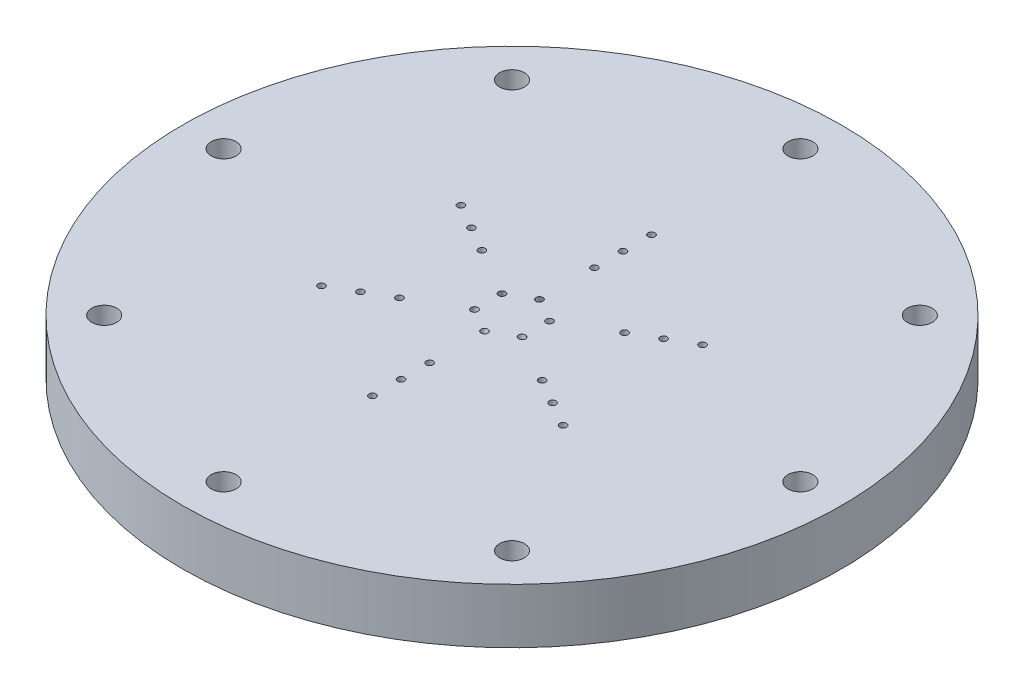
SolidWorks part; units mm, degrees
ref_plane "Front Plane" through (0, 0, 0) normal (0, 0, 1) x (1, 0, 0)
ref_plane "Top Plane" through (0, 0, 0) normal (0, 1, 0) x (1, 0, 0)
ref_plane "Right Plane" through (0, 0, 0) normal (1, 0, 0) x (0, 0, -1)
sketch "Sketch1" plane through (0, 0, 0) normal (0, 1, 0) x (1, 0, 0)
  circle A0 centre (0, 0) radius 38.1
  dimension "D1" = 76.2
extrude "Boss-Extrude1" add sketch "Sketch1" along normal blind 6.35
sketch "Sketch2" plane through (0, 0, 0) normal (0, -1, 0) x (1, 0, 0)
  circle A0 centre (0, 0) radius 33.3375
  circle A1 centre (0, 33.3375) radius 0.762
  dimension "D1" = 66.675
hole_wizard "CBORE for #4 Button Head Cap Screw1" positions "Sketch5" profile "Sketch4" counterbore size "#4" standard "ANSI Inch" end condition through all
sketch "Sketch5" plane through (0, 0, 0) normal (0, -1, 0) x (-1, 0, 0)
  point P0 (0, -33.3375)
sketch "Sketch4" plane through (0, 0, 33.3375) normal (1, 0, 0) x (0, 0, -1)
  line L0 (0, 0) -> (0, 6.35)
  line L1 (0, 6.35) -> (1.4351, 6.35)
  line L3 (1.4351, 6.35) -> (1.4351, 1.905)
  line L4 (1.4351, 1.905) -> (2.413, 1.905)
  line L5 (2.413, 1.905) -> (2.413, 0)
  line L7 (2.413, 0) -> (0, 0)
  line L11 (0, -6.35) -> (0, 107.95) construction
  dimension "Thru Hole Dia." = 2.8702
  dimension "Thru Hole Depth" = 6.35
  dimension "C'Bore Dia." = 4.826
  dimension "C'Bore Depth" = 1.905
pattern_circular "CirPattern1" count 8 over 360 about axis through (0, 0, 0) along (0, 1, 0) of "CBORE for #4 Button Head Cap Screw1"
sketch "Sketch6" plane through (0, 6.35, 0) normal (0, 1, 0) x (1, 0, 0)
  line L0 (0, 9.525) -> (0, 12.827) construction
  circle A0 centre (0, 9.525) radius 0.3969
  circle A2 centre (0, 12.827) radius 0.3969
  circle A3 centre (0, 16.129) radius 0.3969
  circle A4 centre (8.2489, 4.7625) radius 0.3969
  circle A5 centre (11.1085, 6.4135) radius 0.3969
  circle A6 centre (13.9681, 8.0645) radius 0.3969
  circle A7 centre (8.2489, -4.7625) radius 0.3969
  circle A8 centre (11.1085, -6.4135) radius 0.3969
  circle A9 centre (13.9681, -8.0645) radius 0.3969
  circle A10 centre (0, -9.525) radius 0.3969
  circle A11 centre (0, -12.827) radius 0.3969
  circle A12 centre (0, -16.129) radius 0.3969
  circle A13 centre (-8.2489, -4.7625) radius 0.3969
  circle A14 centre (-11.1085, -6.4135) radius 0.3969
  circle A15 centre (-13.9681, -8.0645) radius 0.3969
  circle A16 centre (-8.2489, 4.7625) radius 0.3969
  circle A17 centre (-11.1085, 6.4135) radius 0.3969
  circle A18 centre (-13.9681, 8.0645) radius 0.3969
  point P42 (0, 0)
  dimension "D1" = 0.7937
  dimension "D2" = 3.302
  dimension "D3" = 9.525
  dimension "D4" = 3
  dimension "D5" = 6
extrude "Cut-Extrude1" cut sketch "Sketch6" against normal through all
sketch "Sketch7" plane through (0, 6.35, 0) normal (0, 1, 0) x (1, 0, 0)
  circle A0 centre (0, 3.175) radius 0.3969
  dimension "D1" = 3.175
  dimension "D2" = 0.7937
sketch "Sketch8" plane through (0, 0, 0) normal (0, -1, 0) x (1, 0, 0)
  circle A0 centre (0, -4.7625) radius 0.3969
  circle A1 centre (0, -3.175) radius 0.3969 construction
  dimension "D1" = 0.7937
  dimension "D2" = 1.5875
sketch3d "3DSketch3"
  line L0 (0, 6.35, -3.175) -> (0, 0, -4.7625)
  point P2 (0, 0, -4.7625)
sweep "Cut-Sweep1" cut profiles "Sketch7" path "3DSketch3"
pattern_circular "CirPattern2" count 6 over 360 about axis through (0, 6.35, 0) along (0, 1, 0) of "Cut-Sweep1"
